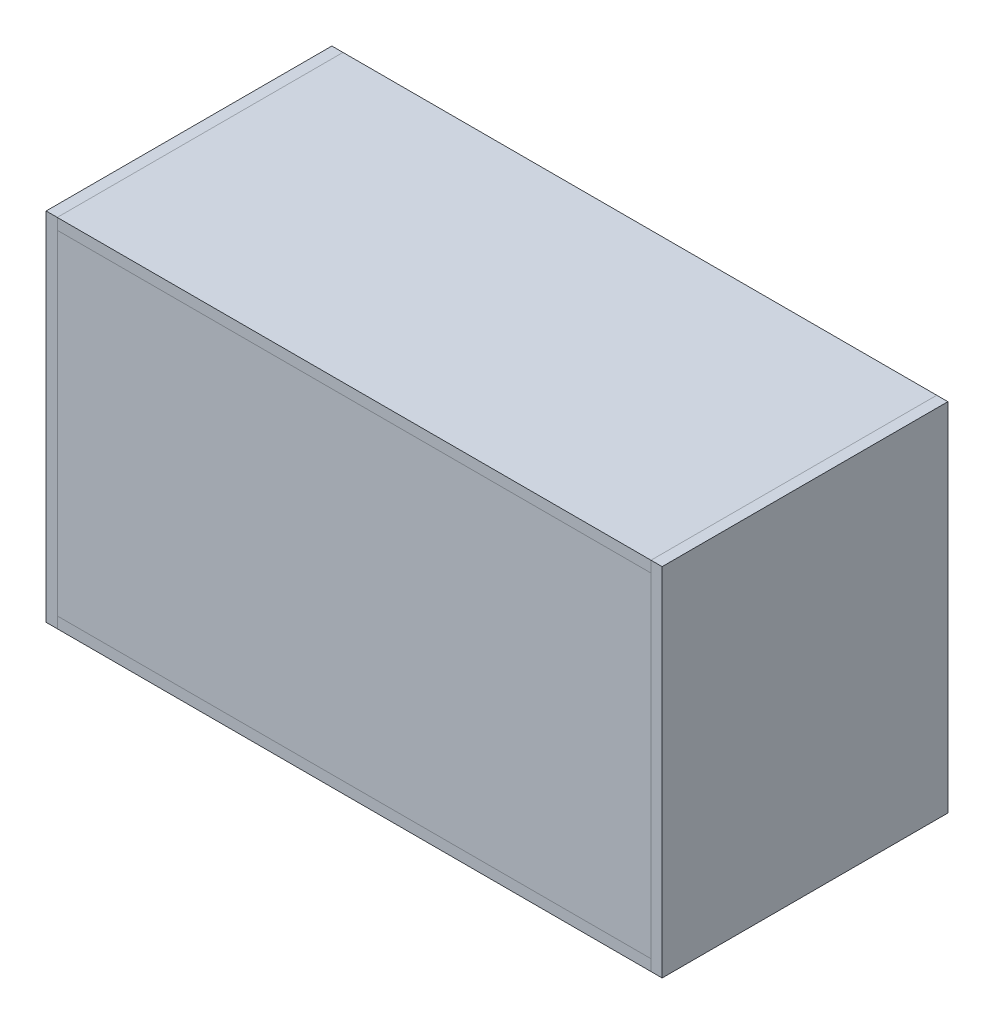
SolidWorks part; units mm, degrees
ref_plane "Front Plane" through (0, 0, 0) normal (0, 0, 1) x (1, 0, 0)
ref_plane "Top Plane" through (0, 0, 0) normal (0, 1, 0) x (1, 0, 0)
ref_plane "Right Plane" through (0, 0, 0) normal (1, 0, 0) x (0, 0, -1)
sketch "Sketch1" plane through (0, 0, 0) normal (0, 1, 0) x (1, 0, 0)
  line L1 (-508, -244.475) -> (508, -244.475)
  line L2 (-508, -244.475) -> (-508, 244.475)
  line L3 (-508, 244.475) -> (508, 244.475)
  line L4 (508, -244.475) -> (508, 244.475)
  line L5 (-508, -244.475) -> (508, 244.475) construction
  line L6 (-508, 244.475) -> (508, -244.475) construction
  point P0 (0, 0)
extrude "bottom" add sketch "Sketch1" against normal blind 19.05
sketch "Sketch2" plane through (-508, 0, 0) normal (-1, 0, 0) x (0, 0, 1)
  line L0 (244.475, -19.05) -> (244.475, 0) construction
  line L2 (-244.475, 590.55) -> (-244.475, -19.05)
  line L3 (-244.475, 590.55) -> (244.475, 590.55)
  line L4 (-244.475, -19.05) -> (244.475, -19.05)
  line L5 (244.475, 590.55) -> (244.475, -19.05)
  line L6 (-244.475, 590.55) -> (244.475, -19.05) construction
  line L7 (-244.475, -19.05) -> (244.475, 590.55) construction
  line L8 (-244.475, -19.05) -> (244.475, -19.05) construction
  point P0 (0, 0)
extrude "side" add sketch "Sketch2" along normal blind 19.05 separate body
mirror "Mirror1" about plane through (0, 0, 0) normal (1, 0, 0) of bodies 114
sketch "Sketch3" plane through (0, 590.55, 0) normal (0, 1, 0) x (1, 0, 0)
  line L1 (-508, -244.475) -> (508, -244.475)
  line L2 (-508, -244.475) -> (-508, 244.475)
  line L3 (-508, 244.475) -> (508, 244.475)
  line L4 (508, -244.475) -> (508, 244.475)
extrude "top" add sketch "Sketch3" against normal blind 19.05 separate body
sketch "Sketch6" plane through (0, 0, 244.475) normal (0, 0, 1) x (1, 0, 0)
  line L0 (508, -19.05) -> (508, 590.55) construction
  line L1 (508, 0) -> (-508, 0)
  line L2 (508, 0) -> (508, 571.5)
  line L3 (508, 571.5) -> (-508, 571.5)
  line L4 (-508, 0) -> (-508, 571.5)
extrude "front" add sketch "Sketch6" against normal blind 19.05 separate body
mirror "Mirror2" about plane through (0, 0, 0) normal (0, 0, 1) of bodies 117
